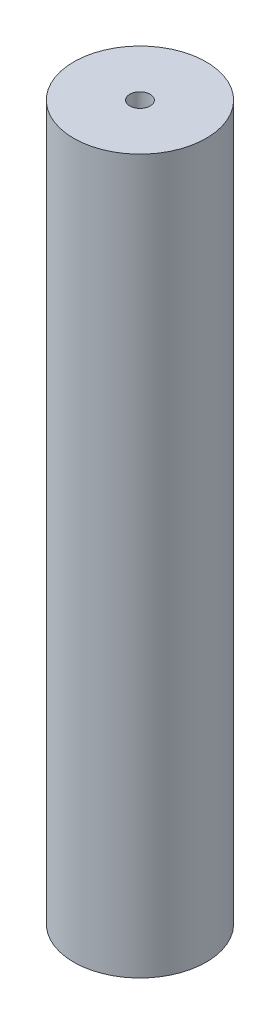
SolidWorks part; units mm, degrees
ref_plane "Front Plane" through (0, 0, 0) normal (0, 0, 1) x (1, 0, 0)
ref_plane "Top Plane" through (0, 0, 0) normal (0, 1, 0) x (1, 0, 0)
ref_plane "Right Plane" through (0, 0, 0) normal (1, 0, 0) x (0, 0, -1)
sketch "Sketch1" plane through (0, 0, 0) normal (0, 1, 0) x (1, 0, 0)
  circle A0 centre (0, 0) radius 6.5
extrude "Boss-Extrude1" add sketch "Sketch1" along normal blind 70
sketch "Sketch2" plane through (0, 70, 0) normal (0, 1, 0) x (1, 0, 0)
  circle A0 centre (0, 0) radius 1
extrude "Cut-Extrude1" cut sketch "Sketch2" against normal through all
